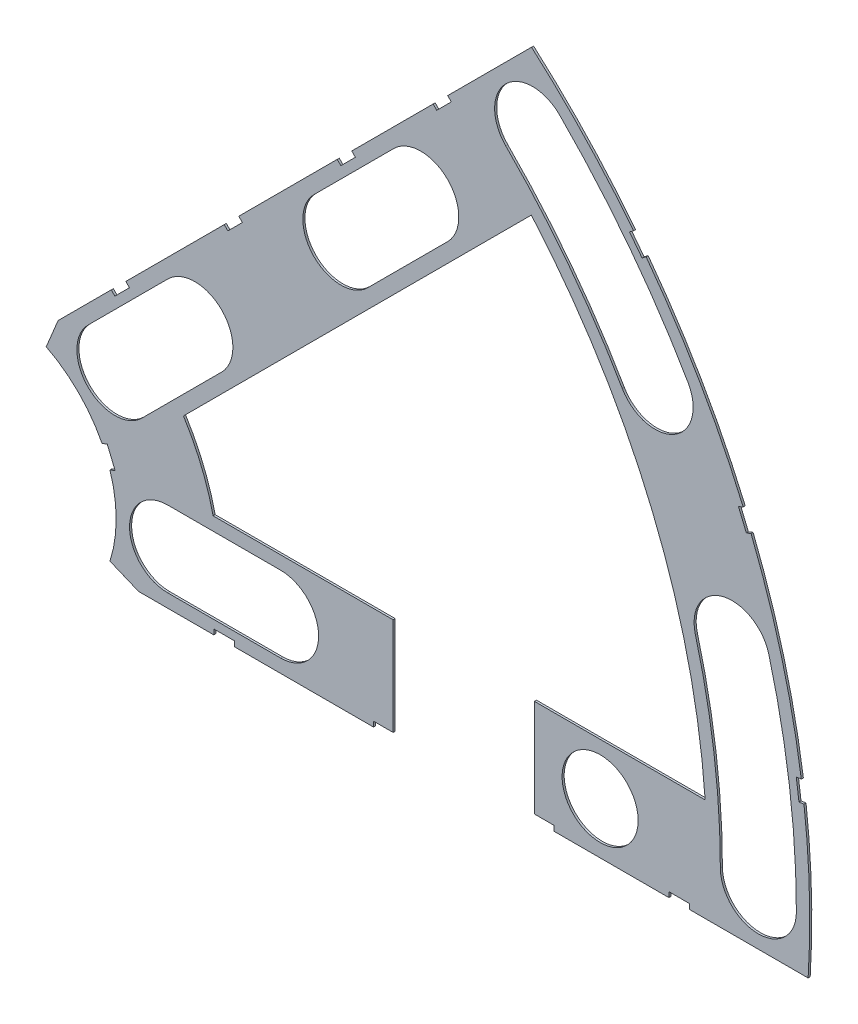
SolidWorks part; units mm, degrees
material "PTFE (general)"
ref_plane "Front Plane" through (0, 0, 0) normal (0, 0, 1) x (1, 0, 0)
ref_plane "Top Plane" through (0, 0, 0) normal (0, 1, 0) x (1, 0, 0)
ref_plane "Right Plane" through (0, 0, 0) normal (1, 0, 0) x (0, 0, -1)
sketch "Sketch1" plane through (0, 0, 0) normal (0, 0, 1) x (1, 0, 0)
  line L0 (0, 0) -> (320.3893, 0) construction
  line L1 (0, 0) -> (155.5285, 155.5285) construction
  line L2 (67.2115, 76.1917) -> (8.6967, 17.6769)
  line L3 (8.6967, 17.6769) -> (7.229, 14.1336)
  line L4 (101.4014, -6.35) -> (18.6489, -6.35)
  line L5 (15.1056, -4.8823) -> (18.6489, -6.35)
  line L6 (88.6729, 6.35) -> (27.8605, 6.35)
  line L9 (67.1914, 58.2111) -> (24.1905, 15.2102)
  line L10 (0, 0) -> (40.4486, 97.6516) construction
  line L11 (0, 0) -> (123.4567, -51.1374) construction
  line L18 (8.6967, 17.6769) -> (13.294, 8.6183) construction
  line L19 (18.6489, -6.35) -> (15.4943, 3.3063) construction
  line L20 (27.8605, 6.35) -> (27.7442, 6.7059) construction
  line L21 (24.1905, 15.2102) -> (24.3599, 14.8764) construction
  arc A0 (7.229, 14.1336) -> (15.1056, -4.8823) centre (0, 0) cw
  arc A1 (67.2115, 76.1917) -> (101.4014, -6.35) centre (0, 0) cw
  arc A2 (24.1905, 15.2102) -> (27.8605, 6.35) centre (0, 0) cw
  arc A3 (67.1914, 58.2111) -> (88.6729, 6.35) centre (0, 0) cw
  arc A8 (13.294, 8.6183) -> (15.4943, 3.3063) centre (0, 0) cw construction
  arc A9 (24.3599, 14.8764) -> (27.7442, 6.7059) centre (0, 0) cw construction
  dimension "D1" = 45
  dimension "D3" = 6.35
  dimension "D4" = 15.875
  dimension "D7" = 22.5
  dimension "D8" = 101.6
  dimension "D11" = 12.7
  dimension "D12" = 12.7
  dimension "D2" = 6.35
  dimension "D5" = 67.5
  dimension "D9" = 1.27
  dimension "D10" = 1.27
  dimension "D6" = 12.7
extrude "Boss-Extrude1" add sketch "Sketch1" along normal blind 0.254
sketch "Sketch2" plane through (0, 0, 0.254) normal (0, 0, 1) x (1, 0, 0)
  line L0 (0, 0) -> (101.6, 0) construction
  line L1 (0, 0) -> (71.842, 71.842) construction
  line L3 (0, 0) -> (22.225, 0) construction
  line L4 (0, 0) -> (15.7154, 15.7154) construction
  line L5 (0, 0) -> (95.25, 0) construction
  line L6 (0, 0) -> (92.0044, 24.6525) construction
  arc A0 (101.4014, -6.35) -> (67.2115, 76.1917) centre (0, 0) ccw construction
  circle A1 centre (22.225, 0) radius 4.699
  arc A2 (15.1056, -4.8823) -> (7.229, 14.1336) centre (0, 0) ccw construction
  circle A3 centre (36.195, 0) radius 4.699
  circle A4 centre (61.722, 0) radius 4.699
  circle A5 centre (75.692, 0) radius 4.699
  circle A6 centre (95.25, 0) radius 4.699
  circle A7 centre (15.7154, 15.7154) radius 4.699
  circle A8 centre (25.5937, 25.5937) radius 4.699
  circle A9 centre (43.644, 43.644) radius 4.699
  circle A10 centre (53.5223, 53.5223) radius 4.699
  circle A11 centre (92.0044, 24.6525) radius 4.699
  circle A12 centre (82.4889, 47.625) radius 4.699
  circle A13 centre (67.3519, 67.3519) radius 4.699
  dimension "D3" = 9.398
  dimension "D1" = 45
  dimension "D2" = 6.35
  dimension "D4" = 6.35
  dimension "D5" = 13.97
  dimension "D7" = 13.97
  dimension "D8" = 19.558
  dimension "D9" = 45
  dimension "D10" = 15
  dimension "D11" = 25.527
  dimension "D6" = 2
extrude "Cut-Extrude1" cut sketch "Sketch2" against normal through all
sketch "Sketch3" plane through (0, 0, 0.254) normal (0, 0, 1) x (1, 0, 0)
  line L0 (15.2664, 24.2467) -> (17.0625, 26.0427)
  line L1 (15.2664, 24.2467) -> (15.7154, 23.7977)
  line L2 (17.0625, 26.0427) -> (17.5115, 25.5937)
  line L3 (15.7154, 23.7977) -> (17.5115, 25.5937)
  line L4 (67.2115, 76.1917) -> (8.6967, 17.6769) construction
  line L5 (44.9911, 53.9713) -> (43.195, 52.1753)
  line L6 (44.9911, 53.9713) -> (45.4401, 53.5223)
  line L7 (43.195, 52.1753) -> (43.644, 51.7263)
  line L8 (45.4401, 53.5223) -> (43.644, 51.7263)
  line L9 (27.94, -6.35) -> (30.48, -6.35)
  line L10 (27.94, -6.35) -> (27.94, -5.715)
  line L11 (30.48, -6.35) -> (30.48, -5.715)
  line L12 (27.94, -5.715) -> (30.48, -5.715)
  line L13 (18.6489, -6.35) -> (101.4014, -6.35) construction
  line L14 (67.437, -6.35) -> (69.977, -6.35)
  line L15 (67.437, -6.35) -> (67.437, -5.715)
  line L16 (69.977, -6.35) -> (69.977, -5.715)
  line L17 (67.437, -5.715) -> (69.977, -5.715)
  line L18 (29.2307, 38.211) -> (31.0268, 40.007)
  line L19 (29.2307, 38.211) -> (29.6797, 37.762)
  line L20 (31.0268, 40.007) -> (31.4758, 39.558)
  line L21 (29.6797, 37.762) -> (31.4758, 39.558)
  line L22 (56.845, 65.8253) -> (55.049, 64.0292)
  line L23 (56.845, 65.8253) -> (57.294, 65.3763)
  line L24 (55.049, 64.0292) -> (55.498, 63.5802)
  line L25 (57.294, 65.3763) -> (55.498, 63.5802)
  line L26 (47.6885, -6.35) -> (50.2285, -6.35)
  line L27 (47.6885, -6.35) -> (47.6885, -5.715)
  line L28 (50.2285, -6.35) -> (50.2285, -5.715)
  line L29 (47.6885, -5.715) -> (50.2285, -5.715)
  line L30 (84.201, -6.35) -> (86.741, -6.35)
  line L31 (84.201, -6.35) -> (84.201, -5.715)
  line L32 (86.741, -6.35) -> (86.741, -5.715)
  line L33 (84.201, -5.715) -> (86.741, -5.715)
  line L34 (0, 0) -> (100.7308, 13.2615) construction
  line L35 (0, 0) -> (93.8662, 38.8806) construction
  line L36 (0, 0) -> (80.6047, 61.8502) construction
  line L37 (0, 0) -> (101.6, 0) construction
  line L38 (99.9355, 14.4377) -> (100.267, 11.9194)
  line L39 (99.9355, 14.4377) -> (101.1946, 14.6035)
  line L40 (100.267, 11.9194) -> (101.5261, 12.0852)
  line L41 (101.1946, 14.6035) -> (101.5261, 12.0852)
  line L42 (99.9355, 14.4377) -> (101.5261, 12.0852) construction
  line L43 (100.267, 11.9194) -> (101.1946, 14.6035) construction
  line L44 (93.7655, 37.4643) -> (94.9388, 37.9503)
  line L45 (93.7655, 37.4643) -> (92.7935, 39.811)
  line L46 (94.9388, 37.9503) -> (93.9668, 40.297)
  line L47 (92.7935, 39.811) -> (93.9668, 40.297)
  line L48 (93.7655, 37.4643) -> (93.9668, 40.297) construction
  line L49 (94.9388, 37.9503) -> (92.7935, 39.811) construction
  line L50 (79.3278, 62.4712) -> (80.874, 60.456)
  line L51 (79.3278, 62.4712) -> (80.3354, 63.2443)
  line L52 (80.874, 60.456) -> (81.8816, 61.2292)
  line L53 (80.3354, 63.2443) -> (81.8816, 61.2292)
  line L54 (79.3278, 62.4712) -> (81.8816, 61.2292) construction
  line L55 (80.874, 60.456) -> (80.3354, 63.2443) construction
  line L56 (13.5939, 7.0054) -> (14.5659, 4.6588)
  line L57 (13.5939, 7.0054) -> (14.7672, 7.4914)
  line L58 (14.5659, 4.6588) -> (15.7393, 5.1448)
  line L59 (14.7672, 7.4914) -> (15.7393, 5.1448)
  line L60 (13.5939, 7.0054) -> (15.7393, 5.1448) construction
  line L61 (14.5659, 4.6588) -> (14.7672, 7.4914) construction
  circle A0 centre (15.7154, 15.7154) radius 4.699 construction
  circle A1 centre (43.644, 43.644) radius 4.699 construction
  circle A2 centre (22.225, 0) radius 4.699 construction
  circle A3 centre (61.722, 0) radius 4.699 construction
  arc A4 (101.4014, -6.35) -> (67.2115, 76.1917) centre (0, 0) ccw construction
  arc A9 (15.1056, -4.8823) -> (7.229, 14.1336) centre (0, 0) ccw construction
  circle A10 centre (36.195, 0) radius 4.699 construction
  circle A11 centre (75.692, 0) radius 4.699 construction
  circle A12 centre (25.5937, 25.5937) radius 4.699 construction
  circle A13 centre (53.5223, 53.5223) radius 4.699 construction
  point P75 (14.6666, 6.0751)
  dimension "D2" = 5.715
  dimension "D3" = 2.54
  dimension "D6" = 5.715
  dimension "D8" = 0.635
  dimension "D9" = 5.715
  dimension "D12" = 5.715
  dimension "D4" = 7.5
  dimension "D5" = 22.5
  dimension "D7" = 37.5
  dimension "D10" = 90
  dimension "D11" = 1.27
  dimension "D14" = 0.635
  dimension "D15" = 90
  dimension "D18" = 0.635
  dimension "D19" = 90
  dimension "D22" = 0.635
  dimension "D20" = 1.27
  dimension "D17" = 0.635
  dimension "D13" = 11.4935
  dimension "D16" = 8.509
  dimension "D21" = 11.4935
  dimension "D23" = 8.509
extrude "Cut-Extrude2" cut sketch "Sketch3" against normal through all
sketch "Sketch5" plane through (0, 0, 0.254) normal (0, 0, 1) x (1, 0, 0)
  line L0 (47.6885, -5.715) -> (47.6885, -6.35) construction
  line L1 (50.1015, -7.62) -> (67.564, -7.62)
  line L2 (50.1015, -7.62) -> (50.1015, 7.62)
  line L4 (50.1015, 7.62) -> (67.564, 7.62)
  line L5 (67.564, -7.62) -> (67.564, 7.62)
  line L8 (69.977, -6.35) -> (69.977, -5.715) construction
  line L9 (50.2285, -6.35) -> (67.437, -6.35) construction
  line L10 (27.8605, 6.35) -> (88.6729, 6.35) construction
  dimension "D1" = 2.413
  dimension "D2" = 2.413
  dimension "D3" = 1.27
  dimension "D4" = 1.27
sketch "Sketch6" plane through (0, 0, 0.254) normal (0, 0, 1) x (1, 0, 0)
  line L0 (0, 0) -> (101.6, 0) construction
  line L1 (0, 0) -> (71.842, 71.842) construction
  line L2 (0, 0) -> (87.9882, 50.8) construction
  line L3 (0, 0) -> (98.1381, 26.296) construction
  line L4 (15.7154, 15.7154) -> (25.5937, 25.5937) construction
  line L5 (12.3928, 19.0381) -> (22.271, 28.9164)
  line L6 (19.0381, 12.3928) -> (28.9164, 22.271)
  line L7 (43.644, 43.644) -> (53.5223, 53.5223) construction
  line L8 (40.3213, 46.9667) -> (50.1996, 56.845)
  line L9 (46.9667, 40.3213) -> (56.845, 50.1996)
  line L10 (22.225, 0) -> (36.195, 0) construction
  line L11 (22.225, 4.699) -> (36.195, 4.699)
  line L12 (22.225, -4.699) -> (36.195, -4.699)
  arc A0 (79.8253, 62.8529) -> (67.2115, 76.1917) centre (0, 0) ccw construction
  arc A1 (12.3928, 19.0381) -> (19.0381, 12.3928) centre (15.7154, 15.7154) ccw
  arc A2 (28.9164, 22.271) -> (22.271, 28.9164) centre (25.5937, 25.5937) ccw
  arc A3 (40.3213, 46.9667) -> (46.9667, 40.3213) centre (43.644, 43.644) ccw
  arc A4 (56.845, 50.1996) -> (50.1996, 56.845) centre (53.5223, 53.5223) ccw
  arc A5 (101.4014, -6.35) -> (100.8887, 12.0013) centre (0, 0) ccw construction
  arc A6 (22.225, 4.699) -> (22.225, -4.699) centre (22.225, 0) ccw
  arc A7 (93.3728, 40.0509) -> (81.3715, 60.8378) centre (0, 0) ccw construction
  arc A8 (100.5572, 14.5196) -> (94.3448, 37.7043) centre (0, 0) ccw construction
  arc A9 (36.195, -4.699) -> (36.195, 4.699) centre (36.195, 0) ccw
  circle A10 centre (53.5223, 53.5223) radius 4.699 construction
  circle A11 centre (25.5937, 25.5937) radius 4.699 construction
  arc A12 (95.25, 0) -> (92.0044, 24.6525) centre (0, 0) ccw construction
  arc A13 (99.949, 0) -> (96.5433, 25.8687) centre (0, 0) ccw
  arc A14 (90.551, 0) -> (87.4655, 23.4363) centre (0, 0) ccw
  arc A15 (90.551, 0) -> (99.949, 0) centre (95.25, 0) ccw
  arc A16 (96.5433, 25.8687) -> (87.4655, 23.4363) centre (92.0044, 24.6525) ccw
  arc A17 (82.4889, 47.625) -> (67.3519, 67.3519) centre (0, 0) ccw construction
  arc A18 (86.5584, 49.9745) -> (70.6746, 70.6746) centre (0, 0) ccw
  arc A19 (78.4195, 45.2755) -> (64.0292, 64.0292) centre (0, 0) ccw
  arc A20 (78.4195, 45.2755) -> (86.5584, 49.9745) centre (82.4889, 47.625) ccw
  arc A21 (70.6746, 70.6746) -> (64.0292, 64.0292) centre (67.3519, 67.3519) ccw
  point P4 (20.6546, 20.6546)
  point P13 (48.5832, 48.5832)
  point P37 (29.21, 0)
  point P61 (94.4351, 12.4326)
  point P68 (75.5669, 57.9845)
  dimension "D2" = 9.398
  dimension "D3" = 9.398
  dimension "D1" = 45
  dimension "D4" = 9.398
  dimension "D5" = 9.398
extrude "Cut-Extrude4" cut sketch "Sketch6" against normal through all
extrude "Cut-Extrude5" cut sketch "Sketch5" against normal through all
equation "\"cSep\"= 1.005"
equation "\"D11@Sketch2\"=\"cSep\""
equation "\"cSep2\"= \"D8@Sketch2\""
equation "\"D13@Sketch3\"=\"cSep\"/2-.05"
equation "\"D16@Sketch3\"=\"cSep2\"/2-.05"
equation "\"D21@Sketch3\"=\"cSep\"/2-.05"
equation "\"D23@Sketch3\"=\"cSep2\"/2-.05"
